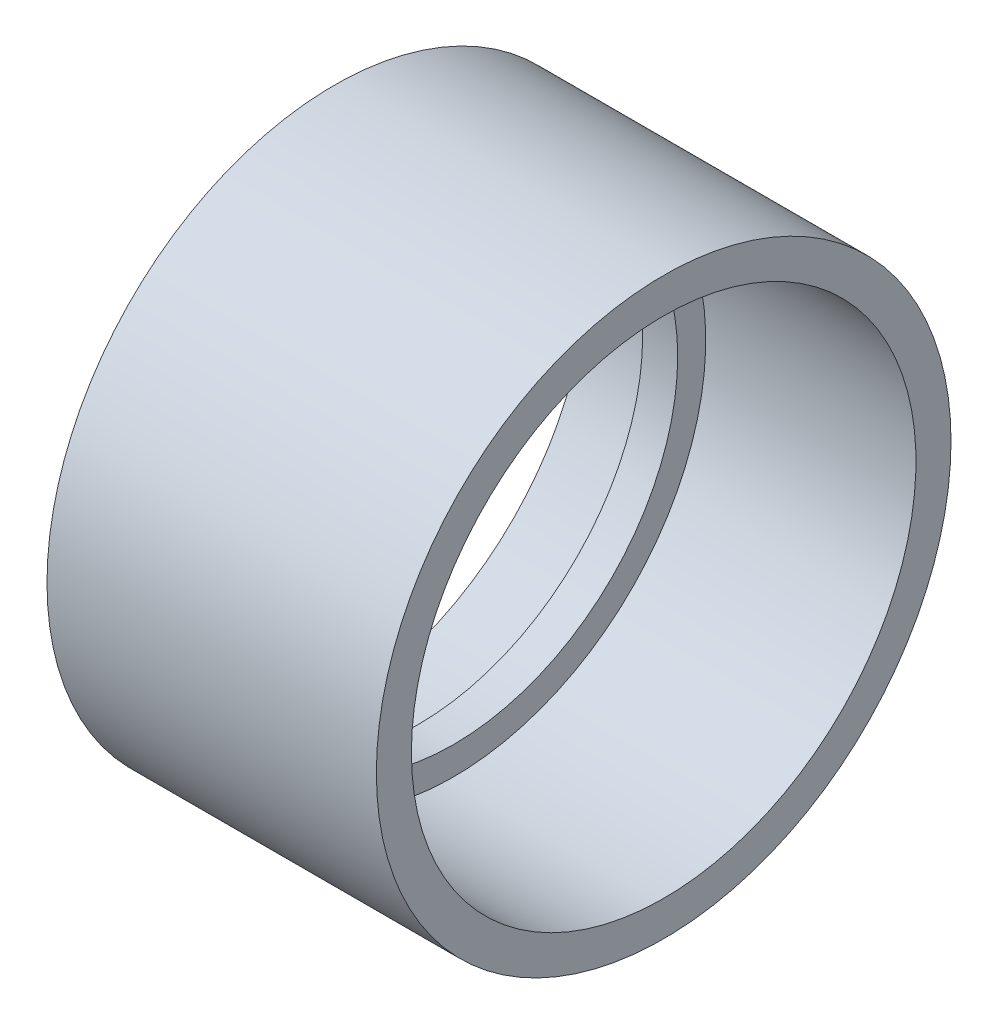
SolidWorks part; units mm, degrees
material "AISI 1020"
ref_plane "Спереди" through (0, 0, 0) normal (0, 0, 1) x (1, 0, 0)
ref_plane "Сверху" through (0, 0, 0) normal (0, 1, 0) x (1, 0, 0)
ref_plane "Справа" through (0, 0, 0) normal (1, 0, 0) x (0, 0, -1)
sketch "Эскиз1" plane through (0, 0, 0) normal (0, 0, 1) x (1, 0, 0)
  line L0 (-1000, 0) -> (49000, 0) construction
  line L1 (-5, 32) -> (0, 32)
  line L2 (-5, -35.4) -> (-5, 35.4) construction
  line L3 (0, 35.4) -> (0, -35.4) construction
  line L4 (0, 32) -> (0, 36)
  line L5 (0, 36) -> (30, 36)
  line L6 (30, 36) -> (30, 41)
  line L7 (30, 41) -> (-17, 41)
  line L8 (-17, 41) -> (-17, 36)
  line L9 (-17, 36) -> (-5, 36)
  line L10 (-5, 36) -> (-5, 32)
  line L11 (-5.6, 36) -> (-17, 36) construction
  line L12 (12, 36) -> (0.6, 36) construction
  line L13 (15, -34.561) -> (15, 34.561) construction
  line L14 (-17, 36) -> (-17, -36) construction
  dimension "D1" = 4
  dimension "D2" = 15
  dimension "D3" = 5
revolve "Повернуть1" add sketch "Эскиз1" angle 360 about L0
